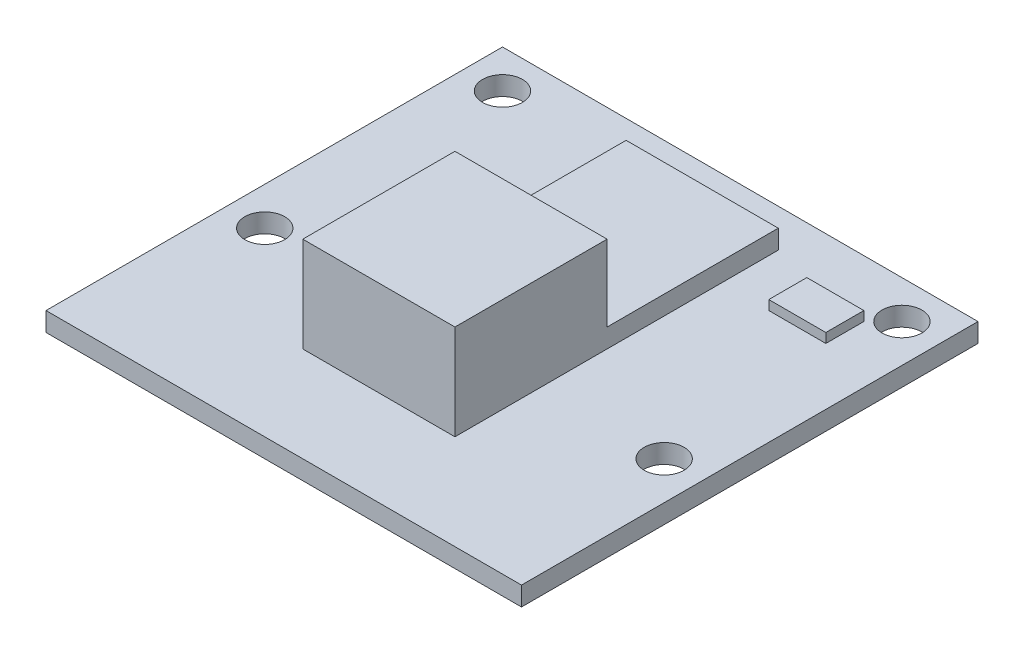
SolidWorks part; units mm, degrees
ref_plane "Front Plane" through (0, 0, 0) normal (0, 0, 1) x (1, 0, 0)
ref_plane "Top Plane" through (0, 0, 0) normal (0, 1, 0) x (1, 0, 0)
ref_plane "Right Plane" through (0, 0, 0) normal (1, 0, 0) x (0, 0, -1)
sketch "Sketch1" plane through (0, 0, 0) normal (0, 1, 0) x (1, 0, 0)
  line L1 (-12.5, 12) -> (12.5, 12)
  line L2 (-12.5, 12) -> (-12.5, -12)
  line L3 (-12.5, -12) -> (12.5, -12)
  line L4 (12.5, 12) -> (12.5, -12)
  line L5 (-12.5, 12) -> (12.5, -12) construction
  line L6 (-12.5, -12) -> (12.5, 12) construction
  point P0 (0, 0)
  dimension "D1" = 25
  dimension "D2" = 24
extrude "Boss-Extrude1" add sketch "Sketch1" along normal blind 1
sketch "Sketch2" plane through (0, 1, 0) normal (0, 1, 0) x (1, 0, 0)
  line L0 (0, 0) -> (0, -50000) construction
  line L1 (-4, 1) -> (4, 1)
  line L2 (-4, 1) -> (-4, -7)
  line L3 (-4, -7) -> (4, -7)
  line L4 (4, 1) -> (4, -7)
  line L5 (-4, 1) -> (4, -7) construction
  line L6 (-4, -7) -> (4, 1) construction
  line L7 (-12.5, -12) -> (12.5, -12) construction
  point P0 (0, -3)
  dimension "D1" = 8
  dimension "D2" = 5
extrude "Boss-Extrude2" add sketch "Sketch2" along normal blind 5
sketch "Sketch3" plane through (0, 1, 0) normal (0, 1, 0) x (1, 0, 0)
  line L1 (-4, 1) -> (4, 1)
  line L2 (-4, 1) -> (-4, 10)
  line L3 (-4, 10) -> (4, 10)
  line L4 (4, 1) -> (4, 10)
  dimension "D1" = 9
extrude "Boss-Extrude3" add sketch "Sketch3" along normal blind 1
sketch "Sketch4" plane through (0, 1, 0) normal (0, 1, 0) x (1, 0, 0)
  line L0 (12.5, -12) -> (12.5, 12) construction
  line L1 (6.5, 9) -> (9.5, 9)
  line L2 (6.5, 9) -> (6.5, 7)
  line L3 (6.5, 7) -> (9.5, 7)
  line L4 (9.5, 9) -> (9.5, 7)
  line L5 (12.5, 12) -> (-12.5, 12) construction
  dimension "D1" = 3
  dimension "D2" = 2
  dimension "D3" = 3
  dimension "D4" = 3
extrude "Boss-Extrude4" add sketch "Sketch4" along normal blind 0.5
sketch "Sketch5" plane through (0, 1, 0) normal (0, 1, 0) x (1, 0, 0)
  line L0 (0, 0) -> (0, 50000) construction
  line L1 (-9.2139, 3.75) -> (49990.7861, 3.75) construction
  line L2 (12.5, 12) -> (-12.5, 12) construction
  circle A0 centre (-10.5, 10) radius 1.0484
  circle A1 centre (10.5, 10) radius 1.0484
  circle A2 centre (10.5, -2.5) radius 1.0484
  circle A3 centre (-10.5, -2.5) radius 1.0484
  dimension "D1" = 21
  dimension "D2" = 12.5
  dimension "D3" = 2
extrude "Cut-Extrude1" cut sketch "Sketch5" against normal up to next
